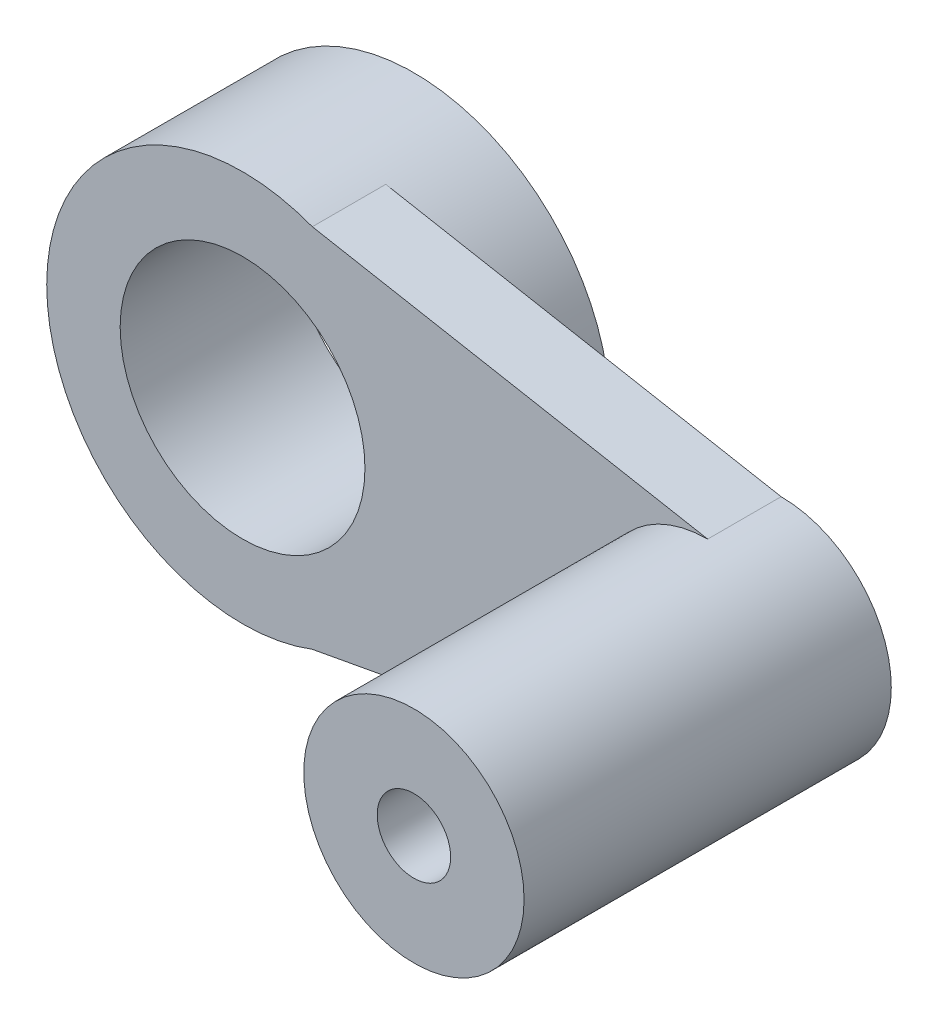
SolidWorks part; units mm, degrees
ref_plane "Front Plane" through (0, 0, 0) normal (0, 0, 1) x (1, 0, 0)
ref_plane "Top Plane" through (0, 0, 0) normal (0, 1, 0) x (1, 0, 0)
ref_plane "Right Plane" through (0, 0, 0) normal (1, 0, 0) x (0, 0, -1)
sketch "Sketch1" plane through (0, 0, 0) normal (0, 0, 1) x (1, 0, 0)
  circle A0 centre (0, 0) radius 10
  circle A1 centre (0, 0) radius 16
  dimension "D1" = 20
extrude "Boss-Extrude1" add sketch "Sketch1" along normal blind 14
sketch "Sketch2" plane through (0, 0, 14) normal (0, 0, 1) x (1, 0, 0)
  line L0 (35, 0) -> (38, 0)
  line L1 (0, 23.2791) -> (0, -26.9249)
  line L2 (38, 18.7847) -> (38, -26.2556)
  line L3 (0, 16) -> (38, 9)
  line L4 (0, -16) -> (38, -9)
  circle A0 centre (38, 0) radius 3
  circle A1 centre (38, 0) radius 9
  circle A2 centre (0, 0) radius 16 construction
  circle M3 centre (0, 0) radius 16
extrude "Boss-Extrude2" add sketch "Sketch2" against normal blind 6 contours A1 L3 L4 M3
sketch "Sketch3" plane through (0, 0, 14) normal (0, 0, 1) x (1, 0, 0)
  circle A0 centre (38, 0) radius 9
  circle A1 centre (38, 0) radius 3
extrude "Boss-Extrude3" add sketch "Sketch3" along normal blind 24 separate body
sketch "Sketch4" plane through (0, 0, 14) normal (0, 0, -1) x (-1, 0, 0)
  circle A0 centre (-38, 0) radius 9
  circle A1 centre (-38, 0) radius 3
extrude "Boss-Extrude4" add sketch "Sketch4" along normal blind 6
